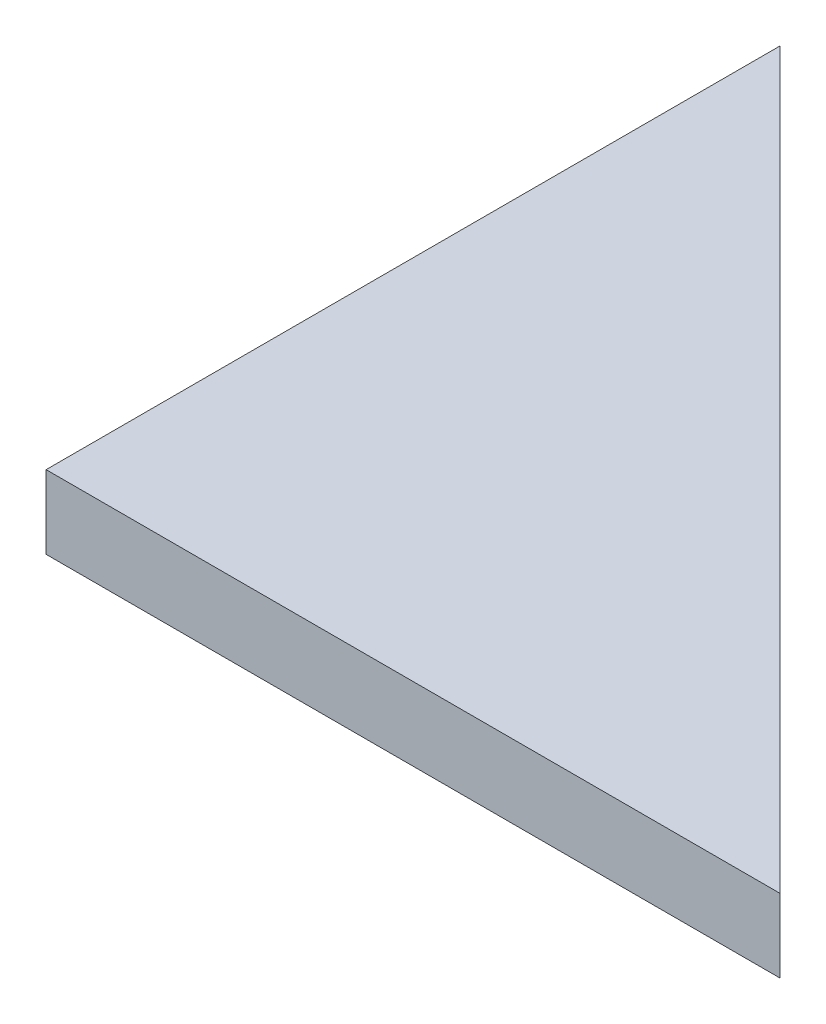
SolidWorks part; units mm, degrees
ref_plane "Front Plane" through (0, 0, 0) normal (0, 0, 1) x (1, 0, 0)
ref_plane "Top Plane" through (0, 0, 0) normal (0, 1, 0) x (1, 0, 0)
ref_plane "Right Plane" through (0, 0, 0) normal (1, 0, 0) x (0, 0, -1)
sketch "Sketch1" plane through (0, 0, 0) normal (0, 1, 0) x (1, 0, 0)
  line L0 (0, 0) -> (0, 50)
  line L1 (0, 50) -> (50, 0)
  line L2 (50, 0) -> (0, 0)
  dimension "D1" = 50
  dimension "D2" = 50
extrude "Boss-Extrude1" add sketch "Sketch1" along normal blind 5
